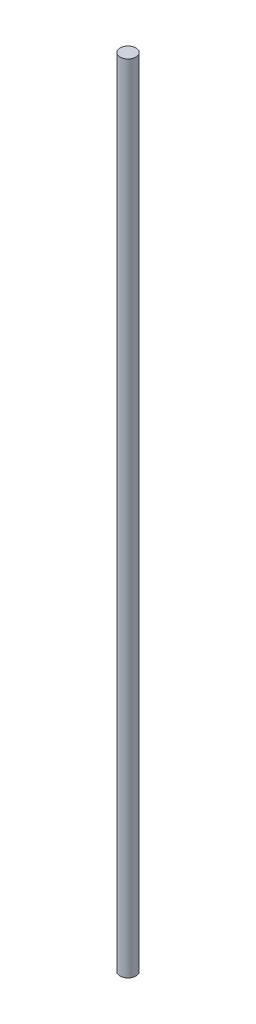
SolidWorks part; units mm, degrees
ref_plane "Płaszczyzna przednia" through (0, 0, 0) normal (0, 0, 1) x (1, 0, 0)
ref_plane "Płaszczyzna górna" through (0, 0, 0) normal (0, 1, 0) x (1, 0, 0)
ref_plane "Płaszczyzna prawa" through (0, 0, 0) normal (1, 0, 0) x (0, 0, -1)
sketch "Sketch1" plane through (0, 0, 0) normal (0, 1, 0) x (1, 0, 0)
  circle A0 centre (0, 0) radius 5
  dimension "D1" = 10
extrude "Boss-Extrude1" add sketch "Sketch1" along normal blind 500
